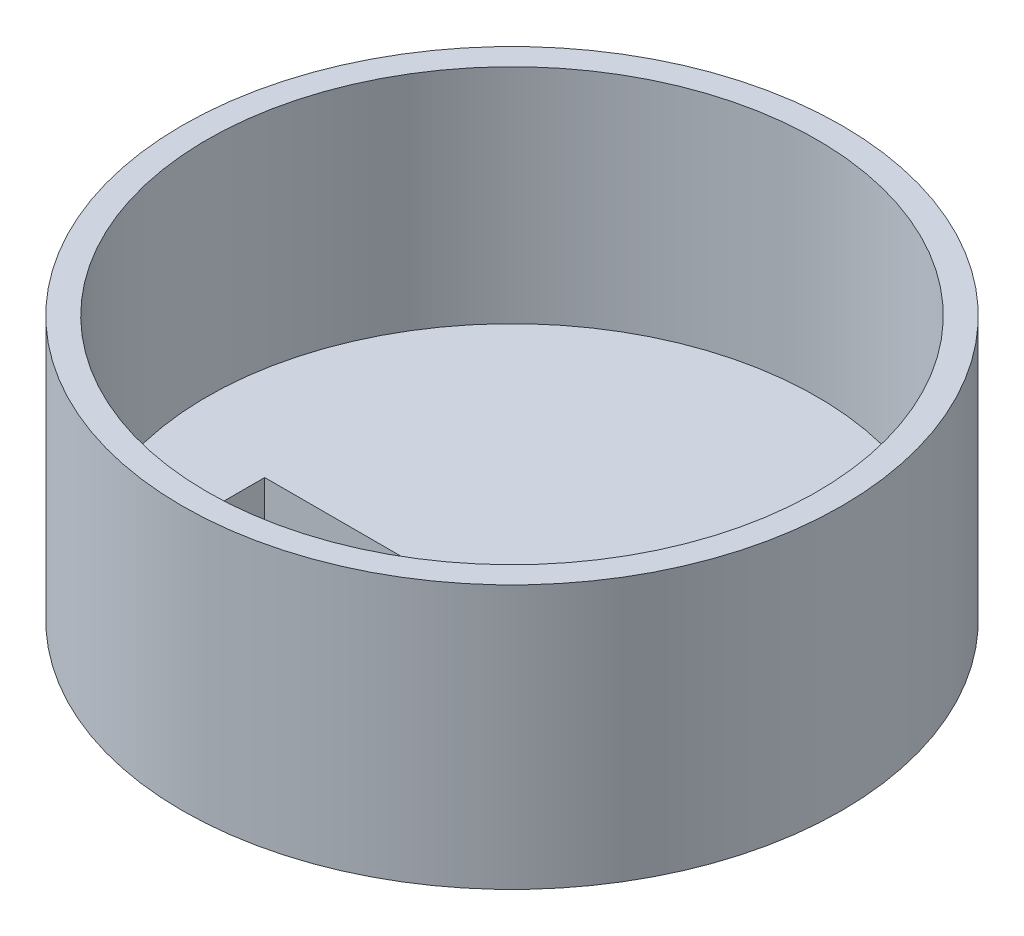
SolidWorks part; units mm, degrees
ref_plane "Front Plane" through (0, 0, 0) normal (0, 0, 1) x (1, 0, 0)
ref_plane "Top Plane" through (0, 0, 0) normal (0, 1, 0) x (1, 0, 0)
ref_plane "Right Plane" through (0, 0, 0) normal (1, 0, 0) x (0, 0, -1)
sketch "Sketch2" plane through (0, 0, 0) normal (0, 1, 0) x (1, 0, 0)
  circle A0 centre (0, 0) radius 40
extrude "Boss-Extrude1" add sketch "Sketch2" along normal blind 30
sketch "Sketch3" plane through (0, 30, 0) normal (0, 1, 0) x (1, 0, 0)
  circle A0 centre (0, 0) radius 37
extrude "Cut-Extrude1" cut sketch "Sketch3" against normal blind 27
sketch "Sketch4" plane through (0, 0, 0) normal (0, -1, 0) x (1, 0, 0)
  line L0 (0, 0) -> (0, 37) construction
  line L1 (37, 0) -> (-37, 0) construction
  line L2 (0, -37) -> (0, 0) construction
  line L4 (-5, -5) -> (5, -5) construction
  line L5 (-5, -5) -> (-5, 5) construction
  line L6 (-5, 5) -> (5, 5) construction
  line L7 (5, -5) -> (5, 5) construction
  line L8 (-5, -5) -> (5, 5) construction
  line L9 (-5, 5) -> (5, -5) construction
  line L10 (5, 5) -> (25, 5)
  line L11 (5, 5) -> (5, 15)
  line L12 (5, 15) -> (25, 15)
  line L13 (25, 5) -> (25, 15)
  line L14 (-5, 5) -> (-25, 5)
  line L15 (-5, 5) -> (-5, 15)
  line L16 (-5, 15) -> (-25, 15)
  line L17 (-25, 5) -> (-25, 15)
  circle A0 centre (0, 0) radius 37 construction
  dimension "D1" = 10
  dimension "D2" = 10
  dimension "D3" = 20
  dimension "D4" = 20
  dimension "D5" = 10
  dimension "D6" = 10
extrude "Cut-Extrude2" cut sketch "Sketch4" along normal blind 10 and the other way blind 10
sketch "Sketch5" plane through (0, 0, 0) normal (0, -1, 0) x (1, 0, 0)
  line L0 (-25, 5) -> (-25, -5.507) construction
  line L1 (-25, -5.507) -> (25, -5.507) construction
  line L2 (25, -5.507) -> (25, 5) construction
  parabola Q0 (-25, -5.507) -> (25.1179, -5.6023) focus (0.3435, -9.3645) apex (0.447, -20.1313) construction
  spline S0 degree 2 poles (-25, -5.507) (0.0969, -22.9398) (25, -5.507) knots 0 0 0 1 1 1 construction
  spline S1 degree 2 poles (25.1179, -5.6023) (0.4511, -48.504) (-25, -5.507) knots 0 0 0 1 1 1 construction
  spline S2 degree 3 poles (0.3072, -46.7753) (-38.1134, 8.6898) (0.0904, -24.3679) (37.6976, 8.4313) (0.3072, -46.7753) (-38.1134, 8.6898) (0.0904, -24.3679) knots -0.775414 -0.554763 -0.280034 0 0.224586 0.445237 0.719966 1 1.224586 1.445237 1.719966 only from (-25, -5.507) to (-25, -5.507)
extrude "Boss-Extrude2" add sketch "Sketch5" along normal blind 2
sketch "Sketch6" plane through (0, 0, 0) normal (0, -1, 0) x (1, 0, 0)
  spline S0 degree 3 poles (3.5327, 18.6023) (1.5946, 10.1029) (-0.1985, -2.1086) (13.6704, 0.5018) (20.6022, 0.457) (30.7787, -1.0433) (29.8532, 6.7295) (29.6566, 12.1805) (31.447, 17.2365) (33.0977, 21.9014) (27.5453, 26.6466) (19.0389, 21.2716) (9.3112, 23.9753) (-0.0907, 23.0939) (-9.3843, 23.9259) (-19.1309, 20.6342) (-27.2655, 26.4098) (-33.2987, 21.7489) (-31.4421, 16.7546) (-30.8238, 11.5243) (-29.2004, 6.2335) (-31.0807, -0.91) (-24.8199, 0.2407) (-19.1478, 0.947) (-12.0432, 0.2245) (-0.603, -1.5895) (-0.4117, 10.0019) (-2.8965, 18.3934) (3.5327, 18.6023) (1.5946, 10.1029) (-0.1985, -2.1086) knots -0.054562 -0.037403 -0.016558 0 0.071645 0.112353 0.167636 0.200468 0.225176 0.260862 0.287097 0.305439 0.328541 0.373353 0.434051 0.473334 0.513735 0.573284 0.616414 0.643022 0.658049 0.690378 0.721297 0.748244 0.765834 0.795667 0.841017 0.874098 0.945438 0.962597 0.983442 1 1.071645 1.112353 1.167636 only from (2.5857, 14.3443) to (2.5857, 14.3443)
  point P0 (-20.0697, 22.5938)
  point P6 (0, 0)
  point P12 (-3.3828, 10.9591)
  point P14 (-3.2818, 15.5029)
  point P16 (-2.575, 4.4967)
  point P18 (3.7864, 0)
  point P20 (-19.4376, 0)
  point P22 (-26.0009, 0)
  point P24 (0, 0)
extrude "Boss-Extrude3" add sketch "Sketch6" along normal blind 1
sketch "Sketch7" plane through (0, -2, 0) normal (0, -1, 0) x (1, 0, 0)
  spline S0 degree 3 poles (-35.359, 5.2478) (-0.0827, -28.8177) (35.1854, 4.9827) (-0.0844, -39.0645) (-35.359, 5.2478) (-0.0827, -28.8177) (35.1854, 4.9827) knots -0.764042 -0.501542 -0.237457 0 0.235958 0.498458 0.762543 1 1.235958 1.498458 1.762543 only from (0, -17.915) to (0, -17.915)
  point P2 (0.8619, -17.7919)
  point P4 (0, -23.8251)
  point P6 (0, -17.915)
extrude "Cut-Extrude3" cut sketch "Sketch7" against normal blind 2
sketch "Sketch8" plane through (0, 0, 0) normal (0, -1, 0) x (1, 0, 0)
  circle A0 centre (0, 0) radius 39
  circle A1 centre (0, 0) radius 40
extrude "Boss-Extrude4" add sketch "Sketch8" along normal blind 2
sketch "Sketch10" plane through (0, -1, 0) normal (0, -1, 0) x (1, 0, 0)
  line L0 (5, 15) -> (25, 15) construction
  line L1 (-3.5, 2.5) -> (-26.5, 2.5)
  line L2 (-3.5, 2.5) -> (-3.5, 17.5)
  line L3 (-3.5, 17.5) -> (-26.5, 17.5)
  line L4 (-26.5, 2.5) -> (-26.5, 17.5)
  line L5 (3.5, 2.5) -> (26.5, 2.5)
  line L6 (3.5, 2.5) -> (3.5, 17.5)
  line L7 (3.5, 17.5) -> (26.5, 17.5)
  line L8 (26.5, 2.5) -> (26.5, 17.5)
  line L9 (-25, 15) -> (-5, 15) construction
  line L10 (-5, 15) -> (-5, 5) construction
  line L11 (5, 5) -> (5, 15) construction
  dimension "D1" = 23
  dimension "D2" = 23
  dimension "D3" = 15
  dimension "D4" = 15
  dimension "D5" = 2.5
  dimension "D6" = 2.5
  dimension "D7" = 1.5
  dimension "D8" = 1.5
extrude "Boss-Extrude5" add sketch "Sketch10" along normal blind 1
sketch "Sketch11" plane through (0, 0, 0) normal (0, 1, 0) x (1, 0, 0)
  line L1 (25, -5) -> (5, -5)
  line L2 (25, -5) -> (25, -15)
  line L3 (25, -15) -> (5, -15)
  line L4 (5, -5) -> (5, -15)
  line L5 (-5, -5) -> (-25, -5)
  line L6 (-5, -5) -> (-5, -15)
  line L7 (-5, -15) -> (-25, -15)
  line L8 (-25, -5) -> (-25, -15)
extrude "Cut-Extrude5" cut sketch "Sketch11" against normal through all
